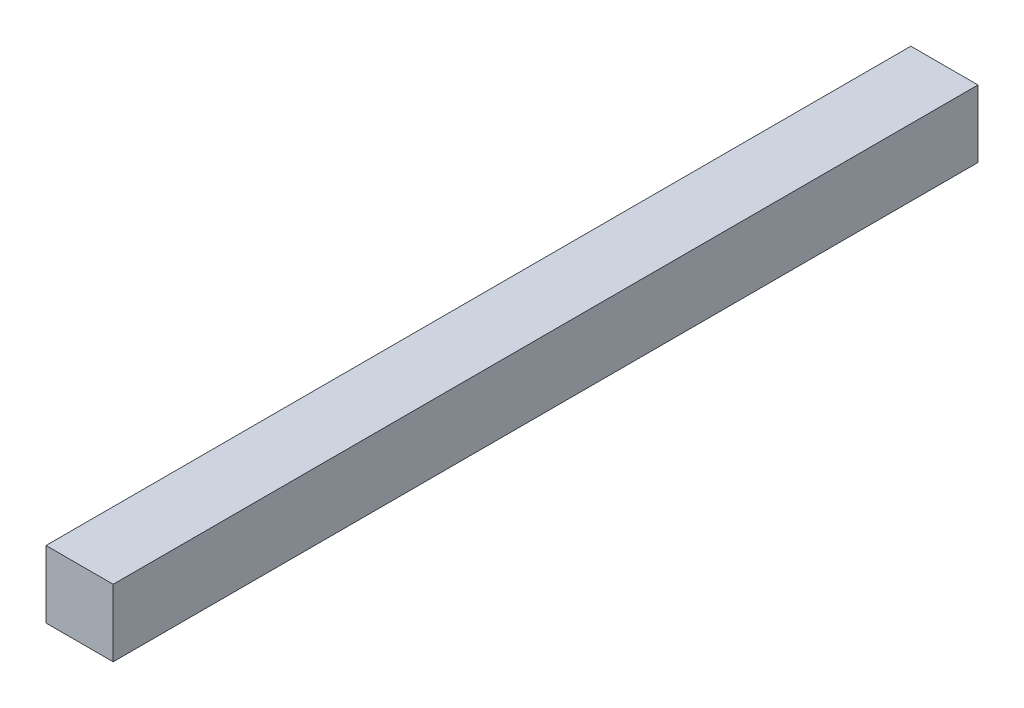
SolidWorks part; units mm, degrees
ref_plane "Front Plane" through (0, 0, 0) normal (0, 0, 1) x (1, 0, 0)
ref_plane "Top Plane" through (0, 0, 0) normal (0, 1, 0) x (1, 0, 0)
ref_plane "Right Plane" through (0, 0, 0) normal (1, 0, 0) x (0, 0, -1)
sketch "Sketch1" plane through (0, 0, 0) normal (0, 0, 1) x (1, 0, 0)
  line L1 (0, 0) -> (25.4, 0)
  line L2 (0, 0) -> (0, 25.4)
  line L3 (0, 25.4) -> (25.4, 25.4)
  line L4 (25.4, 0) -> (25.4, 25.4)
  dimension "D1" = 25.4
  dimension "D2" = 25.4
extrude "Boss-Extrude1" add sketch "Sketch1" along normal blind 327.025
